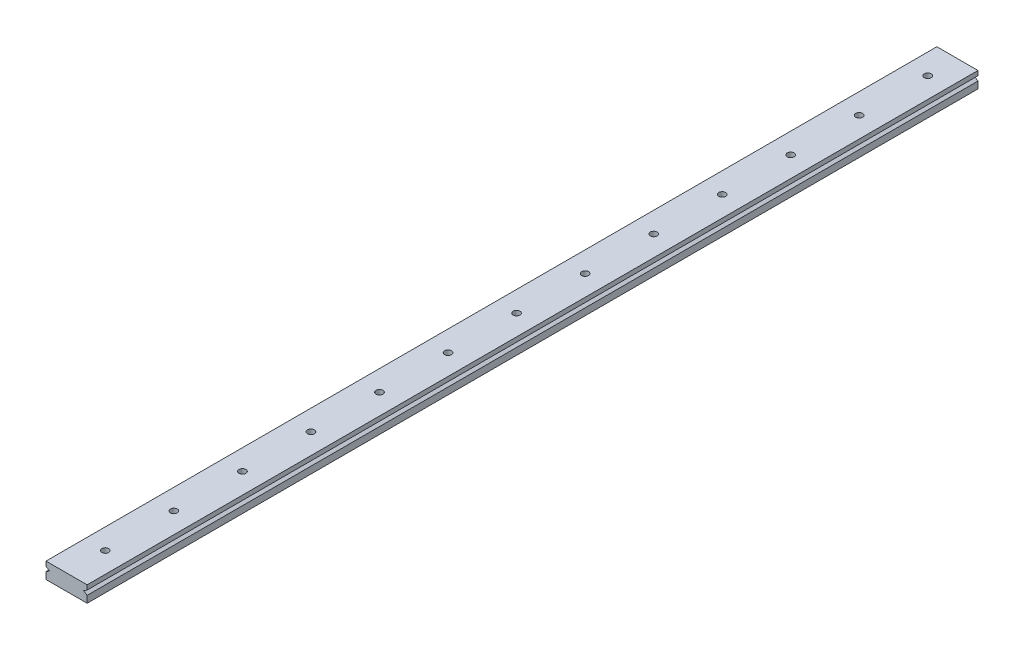
SolidWorks part; units mm, degrees
ref_plane "Front Plane" through (0, 0, 0) normal (0, 0, 1) x (1, 0, 0)
ref_plane "Top Plane" through (0, 0, 0) normal (0, 1, 0) x (1, 0, 0)
ref_plane "Right Plane" through (0, 0, 0) normal (1, 0, 0) x (0, 0, -1)
sketch "Sketch1" plane through (0, 0, 0) normal (0, 0, 1) x (1, 0, 0)
  line L1 (-9, -3.5) -> (9, -3.5)
  line L2 (-9, -3.5) -> (-9, 3.5)
  line L3 (-9, 3.5) -> (9, 3.5)
  line L4 (9, -3.5) -> (9, 3.5)
  line L5 (-9, -3.5) -> (9, 3.5) construction
  line L6 (-9, 3.5) -> (9, -3.5) construction
  point P0 (0, 0)
  dimension "D1" = 18
  dimension "D2" = 7
extrude "Boss-Extrude1" add sketch "Sketch1" along normal blind 390
sketch "Sketch3" plane through (0, 3.5, 0) normal (0, 1, 0) x (1, 0, 0)
  line L1 (9, -390) -> (-9, -390) construction
  circle A0 centre (0, -13) radius 1.5
  circle A1 centre (0, -43) radius 1.5
  circle A2 centre (0, -73) radius 1.5
  circle A4 centre (0, -103) radius 1.5
  circle A5 centre (0, -133) radius 1.5
  circle A6 centre (0, -163) radius 1.5
  circle A7 centre (0, -193) radius 1.5
  circle A9 centre (0, -223) radius 1.5
  circle A10 centre (0, -253) radius 1.5
  circle A11 centre (0, -283) radius 1.5
  circle A12 centre (0, -313) radius 1.5
  circle A13 centre (0, -343) radius 1.5
  circle A14 centre (0, -373) radius 1.5
  point P41 (0, -390)
  dimension "D1" = 3
  dimension "D3" = 3
  dimension "D7" = 30
  dimension "D14" = 30
  dimension "D2" = 13
  dimension "D4" = 30
  dimension "D5" = 30
  dimension "D6" = 30
  dimension "D8" = 30
  dimension "D9" = 30
  dimension "D10" = 30
  dimension "D11" = 30
  dimension "D12" = 30
  dimension "D13" = 30
  dimension "D15" = 30
  dimension "D16" = 17
extrude "Cut-Extrude1" cut sketch "Sketch3" against normal blind 390
sketch "Sketch5" plane through (0, 0, 0) normal (0, 0, -1) x (-1, 0, 0)
  line L0 (9, 3.5) -> (9, -3.5) construction
  line L1 (9, 1.5) -> (7.5, 0.5)
  line L2 (7.5, 0.5) -> (9, -0.5)
  line L3 (9, -0.5) -> (9, 1.5)
  line L4 (0, 0) -> (0, 6.056)
  line L5 (-9, -0.5) -> (-9, 1.5)
  line L6 (-7.5, 0.5) -> (-9, -0.5)
  line L7 (-9, 1.5) -> (-7.5, 0.5)
  point P0 (9, 1.5)
  point P1 (9, -0.5)
  point P5 (9, 0.5)
  point P7 (7.5, 0.5)
  point P17 (-9, 0.5)
  line M5 (-9, 3.5) -> (-9, -3.5)
  line M7 (9, -3.5) -> (9, 3.5)
  dimension "D1" = 2
  dimension "D2" = 3
  dimension "D3" = 1
  dimension "D4" = 1.5
extrude "Cut-Extrude2" cut sketch "Sketch5" against normal blind 390 contours L7 L6 M5 | L1 L2 M7
